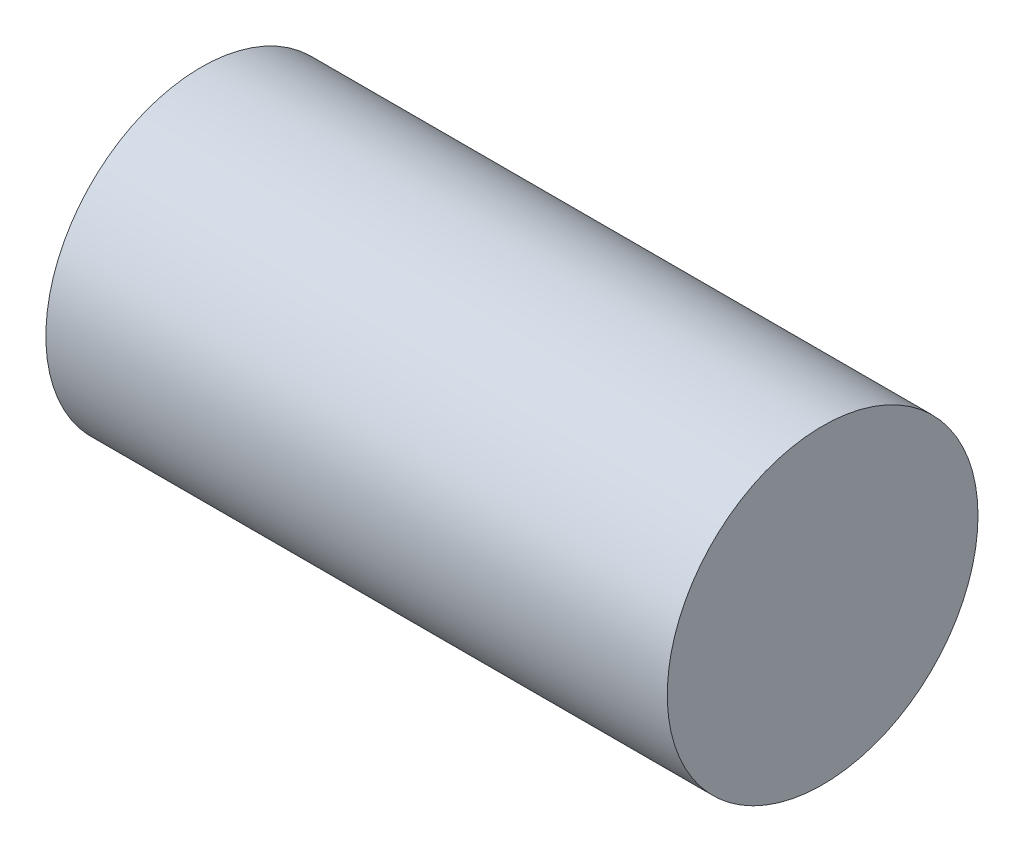
SolidWorks part; units mm, degrees
ref_plane "Front Plane" through (0, 0, 0) normal (0, 0, 1) x (1, 0, 0)
ref_plane "Top Plane" through (0, 0, 0) normal (0, 1, 0) x (1, 0, 0)
ref_plane "Right Plane" through (0, 0, 0) normal (1, 0, 0) x (0, 0, -1)
sketch "Sketch1" plane through (0, 0, 0) normal (1, 0, 0) x (0, 0, -1)
  circle A0 centre (0, 0) radius 5
  dimension "D1" = 10
extrude "Boss-Extrude1" add sketch "Sketch1" along normal blind 20
